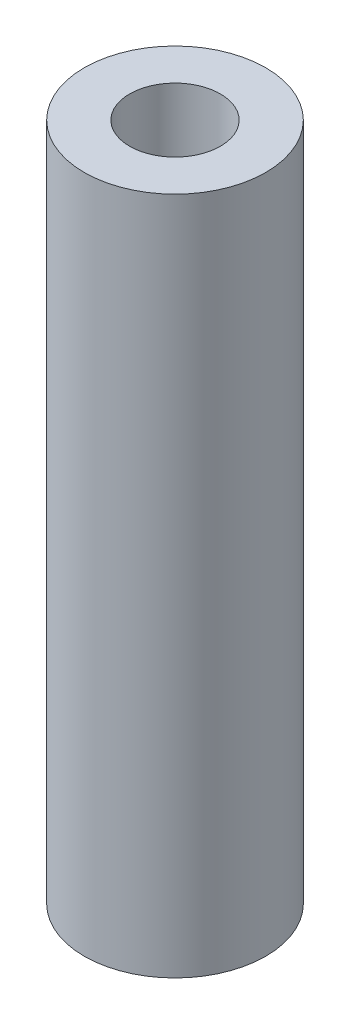
SolidWorks part; units mm, degrees
material "PTFE (general)"
ref_plane "Front Plane" through (0, 0, 0) normal (0, 0, 1) x (1, 0, 0)
ref_plane "Top Plane" through (0, 0, 0) normal (0, 1, 0) x (1, 0, 0)
ref_plane "Right Plane" through (0, 0, 0) normal (1, 0, 0) x (0, 0, -1)
sketch "Sketch1" plane through (0, 0, 0) normal (0, 1, 0) x (1, 0, 0)
  circle A0 centre (0, 0) radius 3.175
  circle A1 centre (0, 0) radius 1.5875
  dimension "D1" = 3.175
  dimension "D2" = 6.35
extrude "Boss-Extrude1" add sketch "Sketch1" along normal blind 23.75
